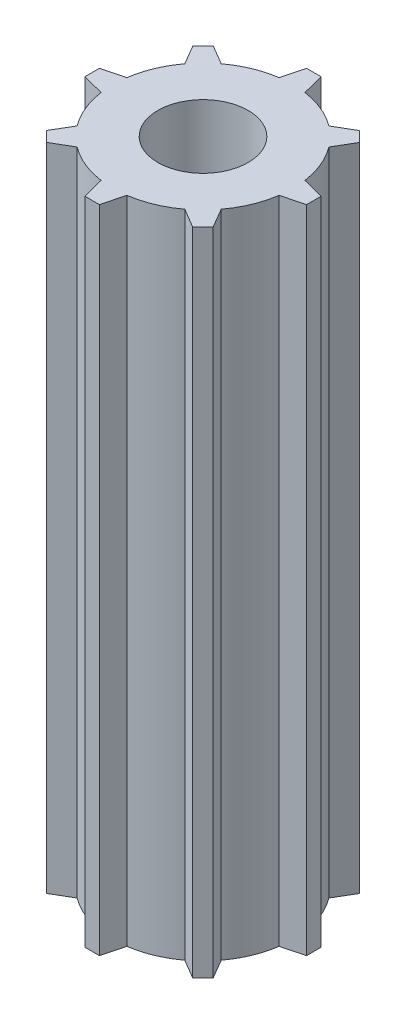
SolidWorks part; units mm, degrees
ref_plane "Front Plane" through (0, 0, 0) normal (0, 0, 1) x (1, 0, 0)
ref_plane "Top Plane" through (0, 0, 0) normal (0, 1, 0) x (1, 0, 0)
ref_plane "Right Plane" through (0, 0, 0) normal (1, 0, 0) x (0, 0, -1)
sketch "Sketch8" plane through (0, 0, 0) normal (0, 1, 0) x (1, 0, 0)
  line L1 (-0.9058, 6.2594) -> (-0.5051, 7.7888)
  line L3 (0.9058, 6.2594) -> (0.5109, 7.7888)
  line L4 (-0.5051, 7.7888) -> (0.5109, 7.7888)
  line L5 (5.0666, 3.7855) -> (5.8688, 5.1462)
  line L6 (3.7855, 5.0666) -> (5.1504, 5.8646)
  line L7 (5.1504, 5.8646) -> (5.8688, 5.1462)
  line L8 (6.2594, -0.9058) -> (7.7888, -0.5109)
  line L9 (6.2594, 0.9058) -> (7.7888, 0.5051)
  line L10 (7.7888, 0.5051) -> (7.7888, -0.5109)
  line L11 (3.7855, -5.0666) -> (5.1462, -5.8688)
  line L12 (5.0666, -3.7855) -> (5.8646, -5.1504)
  line L13 (5.8646, -5.1504) -> (5.1462, -5.8688)
  line L14 (-0.9058, -6.2594) -> (-0.5109, -7.7888)
  line L15 (0.9058, -6.2594) -> (0.5051, -7.7888)
  line L16 (0.5051, -7.7888) -> (-0.5109, -7.7888)
  line L17 (-5.0666, -3.7855) -> (-5.8688, -5.1462)
  line L18 (-3.7855, -5.0666) -> (-5.1504, -5.8646)
  line L19 (-5.1504, -5.8646) -> (-5.8688, -5.1462)
  line L20 (-6.2594, 0.9058) -> (-7.7888, 0.5109)
  line L21 (-6.2594, -0.9058) -> (-7.7888, -0.5051)
  line L22 (-7.7888, -0.5051) -> (-7.7888, 0.5109)
  line L23 (-3.7855, 5.0666) -> (-5.1462, 5.8688)
  line L24 (-5.0666, 3.7855) -> (-5.8646, 5.1504)
  line L25 (-5.8646, 5.1504) -> (-5.1462, 5.8688)
  arc A0 (-0.9058, 6.2594) -> (-3.7855, 5.0666) centre (0, 0) ccw
  arc A1 (-5.0666, 3.7855) -> (-6.2594, 0.9058) centre (0, 0) ccw
  arc A2 (-6.2594, -0.9058) -> (-5.0666, -3.7855) centre (0, 0) ccw
  arc A3 (-3.7855, -5.0666) -> (-0.9058, -6.2594) centre (0, 0) ccw
  arc A4 (0.9058, -6.2594) -> (3.7855, -5.0666) centre (0, 0) ccw
  arc A5 (5.0666, -3.7855) -> (6.2594, -0.9058) centre (0, 0) ccw
  arc A6 (6.2594, 0.9058) -> (5.0666, 3.7855) centre (0, 0) ccw
  arc A7 (3.7855, 5.0666) -> (0.9058, 6.2594) centre (0, 0) ccw
  point P6 (0, 6.3246)
  point P40 (0, 0)
  dimension "D1" = 12.6492
  dimension "D2" = 8
  dimension "D4" = 1.016
extrude "Boss-Extrude4" add sketch "Sketch8" along normal blind 45.72
sketch "Sketch9" plane through (0, 45.72, 0) normal (0, 1, 0) x (1, 0, 0)
  circle A0 centre (0, 0) radius 3.175
  dimension "D1" = 6.35
extrude "Cut-Extrude3" cut sketch "Sketch9" against normal blind 30.48
equation "\"1.8.00in\"=2"
